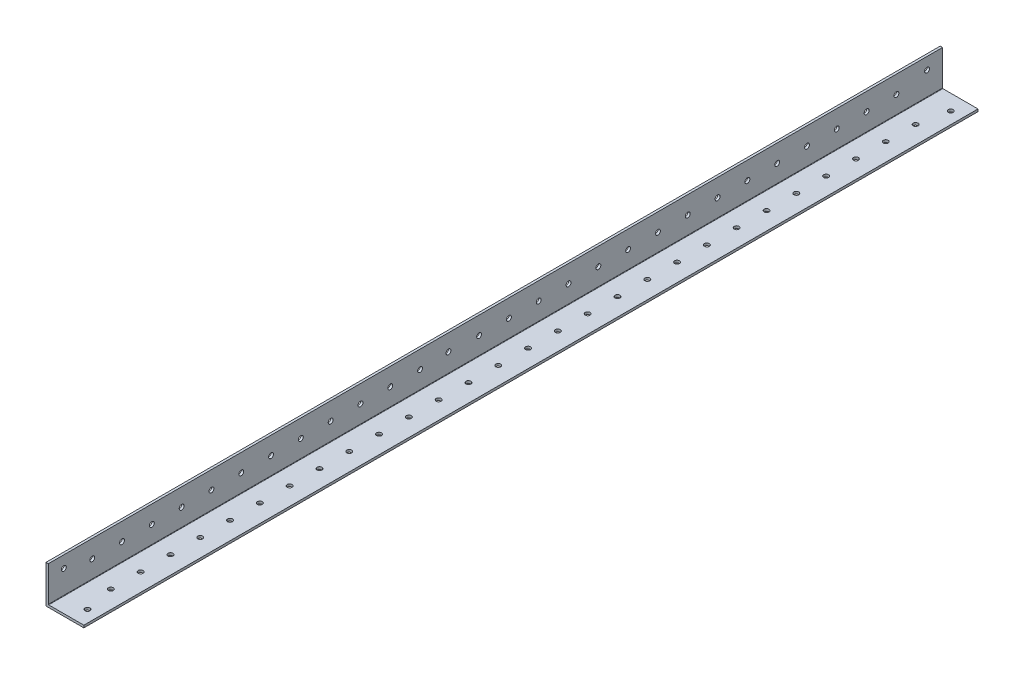
SolidWorks part; units mm, degrees
material "6061 Alloy"
ref_plane "Front Plane" through (0, 0, 0) normal (0, 0, 1) x (1, 0, 0)
ref_plane "Top Plane" through (0, 0, 0) normal (0, 1, 0) x (1, 0, 0)
ref_plane "Right Plane" through (0, 0, 0) normal (1, 0, 0) x (0, 0, -1)
sketch "Sketch1" plane through (0, 0, 0) normal (0, 0, 1) x (1, 0, 0)
  line L0 (0, 25.4) -> (0, 0) construction
  line L1 (0, 0) -> (25.4, 0) construction
  line L2 (25.4, 0) -> (25.4, 1.5875) construction
  line L3 (25.4, 1.5875) -> (1.5875, 1.5875) construction
  line L4 (1.5875, 1.5875) -> (1.5875, 25.4) construction
  line L6 (1.5875, 25.4) -> (0, 25.4) construction
  arc A0 (1.5875, 1.8415) -> (1.8415, 1.5875) centre (1.8415, 1.8415) ccw construction
  point P4 (0, 0)
  dimension "Inside Corner Radius" = 0.254
  dimension "Outside Height" = 25.4
  dimension "Inside Height" = 23.8125
  dimension "Outside Width" = 25.4
  dimension "Inside Width" = 23.8125
  dimension "Wall Thickness" = 1.5875
  dimension "Shape" = 90
sketch "Sketch2" plane through (0, 0, 0) normal (1, 0, 0) x (0, 0, -1)
  line L0 (1219.2, 0) -> (-1219.2, 0) construction
  line L1 (-1219.2, 25.4) -> (-1219.2, 0) construction
  line L2 (1219.2, 25.4) -> (1219.2, 0) construction
  point P0 (-1189.99, 0)
  point P4 (0, 0)
  point P6 (1189.99, 0)
  dimension "D1" = 29.21
  dimension "D2" = 29.21
  dimension "D3" = 25.4
  dimension "Length" = 2438.4
sketch "Sketch3" plane through (0, 0, 0) normal (0, 0, 1) x (1, 0, 0)
  line L0 (1.5875, 25.4) -> (0, 25.4)
  line L1 (0, 25.4) -> (0, 0)
  line L2 (0, 0) -> (25.4, 0)
  line L3 (25.4, 0) -> (25.4, 1.5875)
  line L4 (25.4, 1.5875) -> (1.5875, 1.5875)
  line L5 (1.5875, 1.5875) -> (1.5875, 25.4)
extrude "Boss-Extrude1" add sketch "Sketch3" along normal mid plane 2438.4
fillet "Fillet1" radius 0.254 1 edges at (1.5875, 1.5875, 0)
sketch "Sketch4" plane through (0, 0, 0) normal (-1, 0, 0) x (0, 0, 1)
  line L0 (1219.2, 25.4) -> (1219.2, 0) construction
  line L1 (-1219.2, 0) -> (619.2, 0)
  line L2 (-1219.2, 0) -> (-1219.2, 74.9453)
  line L3 (-1219.2, 74.9453) -> (619.2, 74.9453)
  line L4 (619.2, 0) -> (619.2, 74.9453)
  dimension "D1" = 600
extrude "Cut-Extrude1" cut sketch "Sketch4" against normal blind 60
sketch "Sketch5" plane through (0, 1.5875, 0) normal (0, 1, 0) x (1, 0, 0)
  line L0 (17.4625, -1208.8241) -> (17.4625, -1189.2) construction
  line L1 (13.4937, -649.2) -> (13.4937, -629.5759) construction
  line L3 (1.5875, -1189.2) -> (25.4, -1189.2) construction
  line L4 (1.5875, -1219.2) -> (1.5875, -619.2) construction
  line L5 (25.4, -1219.2) -> (25.4, -619.2) construction
  line L6 (13.4937, -629.5759) -> (17.4625, -629.5759) construction
  line L7 (17.4625, -629.5759) -> (13.4937, -629.5759) construction
  circle A30 centre (17.4625, -629.5759) radius 1.65
  circle A31 centre (17.4625, -1208.8241) radius 1.65
  circle A32 centre (13.4938, -1189.2) radius 1.65
  circle A33 centre (13.4938, -1169.2) radius 1.65
  circle A34 centre (13.4938, -1149.2) radius 1.65
  circle A35 centre (13.4938, -1129.2) radius 1.65
  circle A36 centre (13.4938, -1109.2) radius 1.65
  circle A37 centre (13.4938, -1089.2) radius 1.65
  circle A38 centre (13.4938, -1069.2) radius 1.65
  circle A39 centre (13.4938, -1049.2) radius 1.65
  circle A40 centre (13.4938, -1029.2) radius 1.65
  circle A41 centre (13.4938, -1009.2) radius 1.65
  circle A42 centre (13.4938, -989.2) radius 1.65
  circle A43 centre (13.4938, -969.2) radius 1.65
  circle A44 centre (13.4938, -949.2) radius 1.65
  circle A45 centre (13.4938, -929.2) radius 1.65
  circle A46 centre (13.4938, -909.2) radius 1.65
  circle A47 centre (13.4938, -889.2) radius 1.65
  circle A48 centre (13.4938, -869.2) radius 1.65
  circle A49 centre (13.4938, -849.2) radius 1.65
  circle A50 centre (13.4938, -829.2) radius 1.65
  circle A51 centre (13.4938, -809.2) radius 1.65
  circle A52 centre (13.4938, -789.2) radius 1.65
  circle A53 centre (13.4938, -769.2) radius 1.65
  circle A54 centre (13.4938, -749.2) radius 1.65
  circle A55 centre (13.4938, -729.2) radius 1.65
  circle A56 centre (13.4938, -709.2) radius 1.65
  circle A57 centre (13.4938, -689.2) radius 1.65
  circle A58 centre (13.4938, -669.2) radius 1.65
  circle A59 centre (13.4937, -649.2) radius 1.65
  dimension "D1" = 3.3
  dimension "D2" = 3.3
  dimension "D3" = 28
  dimension "D4" = 20
extrude "Cut-Extrude2" cut sketch "Sketch5" against normal blind 10
sketch "Sketch9" plane through (1.5875, 0, 0) normal (1, 0, 0) x (0, 0, -1)
  line L0 (-1189.7652, 25.4) -> (-1189.7652, 1.5875) construction
  line L1 (-950.7063, 14.2875) -> (-950.7063, 1.5875) construction
  line L2 (-969.7652, 13.4937) -> (-950.7063, 13.4937) construction
  line L3 (-1207.4063, -6.3505) -> (-1204.0063, -6.3505) construction
  line L4 (-634.3937, -3.175) -> (-630.9937, -3.175) construction
  line L5 (-634.3937, 0) -> (-634.3937, -6.35) construction
  line L6 (-630.9937, -6.35) -> (-630.9937, 0) construction
  line L7 (-930.1411, 25.4) -> (-930.1411, 1.5875) construction
  line L8 (-1205.7063, -6.3505) -> (-1205.7063, 14.2875) construction
  line L9 (-1205.7063, 14.2875) -> (-950.7063, 14.2875) construction
  line L10 (-1219.2, 1.5875) -> (-619.2, 1.5875) construction
  line L11 (-950.7063, 5.2366) -> (-930.1411, 5.2366) construction
  line L12 (-1208.8241, 17.4625) -> (-1208.8241, 3.8186) construction
  line L13 (-1215.3265, 3.8186) -> (-1204.9125, 3.8186) construction
  line L14 (-1219.2, 25.4) -> (-619.2, 25.4) construction
  line L15 (-1208.8241, 8.3665) -> (-1189.7652, 8.3665) construction
  line L16 (-629.5759, 17.4625) -> (-629.5759, 3.8186) construction
  line L17 (-623.0735, 3.8186) -> (-633.4875, 3.8186) construction
  line L18 (-650.1411, 13.4937) -> (-629.5759, 13.4937) construction
  circle A0 centre (-629.5759, 17.4625) radius 1.65
  circle A3 centre (-1208.8241, 17.4625) radius 1.65
  circle A46 centre (-950.7063, 14.2875) radius 1.65
  circle A47 centre (-1189.7652, 13.4937) radius 1.65
  circle A48 centre (-1169.7652, 13.4937) radius 1.65
  circle A49 centre (-1149.7652, 13.4937) radius 1.65
  circle A50 centre (-1129.7652, 13.4937) radius 1.65
  circle A51 centre (-1109.7652, 13.4937) radius 1.65
  circle A52 centre (-1089.7652, 13.4937) radius 1.65
  circle A53 centre (-1069.7652, 13.4937) radius 1.65
  circle A54 centre (-1049.7652, 13.4937) radius 1.65
  circle A55 centre (-1029.7652, 13.4937) radius 1.65
  circle A56 centre (-1009.7652, 13.4937) radius 1.65
  circle A57 centre (-989.7652, 13.4937) radius 1.65
  circle A58 centre (-969.7652, 13.4937) radius 1.65
  circle A59 centre (-930.1411, 13.4937) radius 1.65
  circle A60 centre (-910.1411, 13.4937) radius 1.65
  circle A61 centre (-890.1411, 13.4937) radius 1.65
  circle A62 centre (-870.1411, 13.4937) radius 1.65
  circle A63 centre (-850.1411, 13.4937) radius 1.65
  circle A64 centre (-830.1411, 13.4937) radius 1.65
  circle A65 centre (-810.1411, 13.4937) radius 1.65
  circle A66 centre (-790.1411, 13.4937) radius 1.65
  circle A67 centre (-770.1411, 13.4937) radius 1.65
  circle A68 centre (-750.1411, 13.4937) radius 1.65
  circle A69 centre (-730.1411, 13.4937) radius 1.65
  circle A70 centre (-710.1411, 13.4937) radius 1.65
  circle A71 centre (-690.1411, 13.4937) radius 1.65
  circle A72 centre (-670.1411, 13.4937) radius 1.65
  circle A73 centre (-650.1411, 13.4937) radius 1.65
  dimension "D1" = 12.7
  dimension "D3" = 3.3
  dimension "D4" = 3.3
  dimension "D7" = 3.3
  dimension "D2" = 255
  dimension "D5" = 20
  dimension "D6" = 12
  dimension "D8" = 20
extrude "Cut-Extrude6" cut sketch "Sketch9" against normal blind 60
equation "\"D1@Boss-Extrude1\"=\"Length@Sketch2\""
equation "\"D1@Sketch2\" = \"Outside Width@Sketch1\" * 1.15"
equation "\"D2@Sketch2\"=\"D1@Sketch2\""
equation "\"D1@Fillet1\"=\"Inside Corner Radius@Sketch1\""
equation "\"D3@Sketch2\"=\"Outside Height@Sketch1\""
